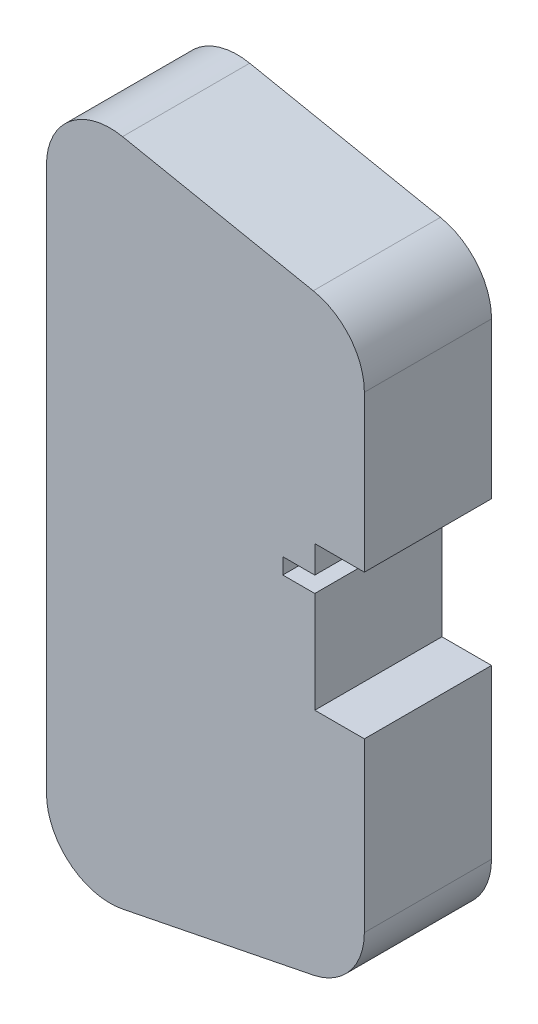
SolidWorks part; units mm, degrees
material "Polyurethane Foam Rigid"
ref_plane "Front Plane" through (0, 0, 0) normal (0, 0, 1) x (1, 0, 0)
ref_plane "Top Plane" through (0, 0, 0) normal (0, 1, 0) x (1, 0, 0)
ref_plane "Right Plane" through (0, 0, 0) normal (1, 0, 0) x (0, 0, -1)
sketch "Sketch1" plane through (0, 0, 0) normal (0, 0, 1) x (1, 0, 0)
  line L0 (0, 72.2334) -> (0, -72.2334) construction
  line L1 (0, 42.802) -> (0, -42.802)
  line L2 (-50, 0) -> (50, 0) construction
  line L3 (11.9612, 52.6078) -> (41.9612, 46.6078)
  line L4 (50, -36.802) -> (50, 36.802)
  line L5 (41.9612, -46.6078) -> (11.9612, -52.6078)
  arc A0 (41.9612, -46.6078) -> (50, -36.802) centre (40, -36.802) ccw
  arc A1 (41.9612, 46.6078) -> (50, 36.802) centre (40, 36.802) cw
  arc A2 (0, -42.802) -> (11.9612, -52.6078) centre (10, -42.802) ccw
  arc A3 (0, 42.802) -> (11.9612, 52.6078) centre (10, 42.802) cw
  point P3 (0, 0)
  point P8 (0, 0)
  point P13 (50, 0)
  point P14 (50, -45)
  point P17 (50, 45)
  point P20 (0, -55)
  point P23 (0, 55)
  dimension "D4" = 10
  dimension "D5" = 10
  dimension "D1" = 50
  dimension "D2" = 110
  dimension "D3" = 90
extrude "Boss-Extrude1" add sketch "Sketch1" along normal blind 20
sketch "Sketch5" plane through (0, 0, 0) normal (-1, 0, 0) x (0, 0, 1)
  line L0 (10, 42.802) -> (10, -42.802) construction
  line L3 (20, 42.802) -> (0, 42.802) construction
  line L4 (20, -42.802) -> (0, -42.802) construction
  line L5 (5.5, 15.8428) -> (14.5, 15.8428)
  line L6 (5.5, 15.8428) -> (5.5, 17.2971)
  line L7 (5.5, 17.2971) -> (14.5, 17.2971)
  line L8 (14.5, 17.2971) -> (14.5, 15.8428)
  point P8 (10, 15.8428)
  point P9 (10, 17.2971)
  dimension "D1" = 9
extrude "Cut-Extrude4" cut sketch "Sketch5" against normal blind 10
sketch "Sketch6" plane through (0, 17.2971, 0) normal (0, -1, 0) x (1, 0, 0)
  line L0 (0, 10) -> (10.2544, 10) construction
  line L1 (0, 14.5) -> (0, 5.5) construction
  circle A0 centre (2.6449, 10) radius 0.5
extrude "Cut-Extrude5" cut sketch "Sketch6" against normal blind 5
sketch "Sketch9" plane through (0, 0, 20) normal (0, 0, 1) x (1, 0, 0)
  line L4 (50, -36.802) -> (50, 36.802) construction
  line L5 (42.2, 5.4971) -> (42.2, -10.4029)
  line L6 (42.2, 7.9971) -> (42.2, 12.2971)
  line L7 (42.2, 12.2971) -> (50, 12.2971)
  line L9 (42.2, -10.4029) -> (50, -10.4029)
  line L10 (37.17, 5.4971) -> (37.17, 7.9971)
  line L11 (42.2, 5.4971) -> (37.17, 5.4971)
  line L12 (37.17, 7.9971) -> (42.2, 7.9971)
  line L13 (50, 12.2971) -> (50, -10.4029)
  point P9 (42.2, -10.4029)
  point P10 (42.2, 5.4971)
  dimension "D2" = 7.8
  dimension "D3" = 5.03
extrude "Cut-Extrude6" cut sketch "Sketch9" against normal through all
sketch "Sketch11" plane through (0, 7.9971, 0) normal (0, -1, 0) x (-1, 0, 0)
  line L0 (-42.2, -10) -> (-37.17, -10) construction
  line L1 (-42.2, 0) -> (-42.2, -20) construction
  line L2 (-37.17, 0) -> (-37.17, -20) construction
  circle A0 centre (-39.9, -10) radius 1
  dimension "D1" = 2
  dimension "D2" = 2.3
extrude "Cut-Extrude7" cut sketch "Sketch11" against normal blind 5
